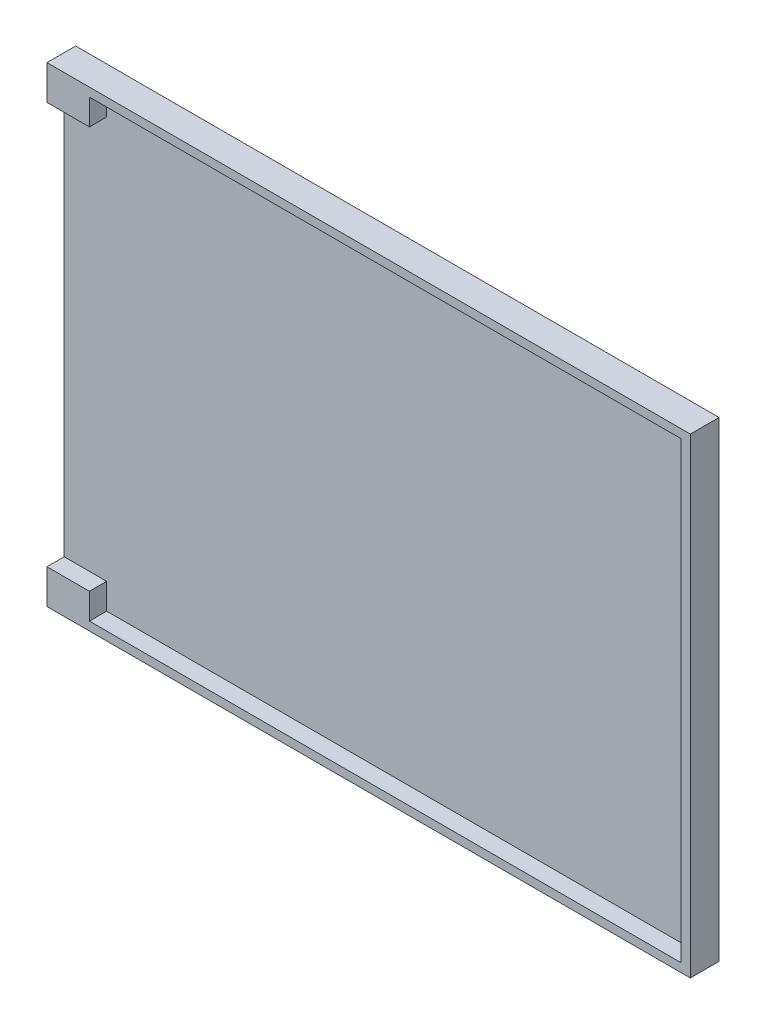
SolidWorks part; units mm, degrees
ref_plane "Front Plane" through (0, 0, 0) normal (0, 0, 1) x (1, 0, 0)
ref_plane "Top Plane" through (0, 0, 0) normal (0, 1, 0) x (1, 0, 0)
ref_plane "Right Plane" through (0, 0, 0) normal (1, 0, 0) x (0, 0, -1)
sketch "Sketch1" plane through (0, 0, 0) normal (0, 0, 1) x (1, 0, 0)
  line L0 (-33.7542, -31.1542) -> (33.4958, -31.1542) construction
  line L2 (33.4958, -31.1542) -> (33.4958, 11.3458) construction
  line L3 (-27.8542, 10.5958) -> (28.1458, 10.5958)
  line L4 (-27.8542, 10.5958) -> (-27.8542, -30.4042)
  line L5 (-27.8542, -30.4042) -> (28.1458, -30.4042)
  line L6 (28.1458, 10.5958) -> (28.1458, -30.4042)
  point P6 (0, 0)
  dimension "D1" = 41
  dimension "D2" = 56
  dimension "D3" = 0.75
  dimension "D4" = 5.35
extrude "Boss-Extrude1" add sketch "Sketch1" along normal blind 2.5
sketch "Sketch2" plane through (0, 0, 2.5) normal (0, 0, 1) x (1, 0, 0)
  line L1 (-24.1542, 9.8458) -> (27.3458, 9.8458)
  line L2 (-24.1542, 9.8458) -> (-24.1542, -29.6542)
  line L3 (-24.1542, -29.6542) -> (27.3458, -29.6542)
  line L4 (27.3458, 9.8458) -> (27.3458, -29.6542)
  line L5 (28.1458, 10.5958) -> (28.1458, -30.4042) construction
  point P4 (28.1458, -9.9042)
  point P5 (27.3458, -9.9042)
  dimension "D1" = 39.5
  dimension "D2" = 51.5
  dimension "D3" = 0.8
extrude "Cut-Extrude1" cut sketch "Sketch2" against normal blind 1.5
sketch "Sketch3" plane through (0, 0, 2.5) normal (0, 0, 1) x (1, 0, 0)
  line L0 (-27.8542, 10.5958) -> (-27.8542, -30.4042) construction
  line L1 (-27.8542, 7.5958) -> (-24.1542, 7.5958)
  line L2 (-27.8542, 7.5958) -> (-27.8542, -27.4042)
  line L3 (-27.8542, -27.4042) -> (-24.1542, -27.4042)
  line L4 (-24.1542, 7.5958) -> (-24.1542, -27.4042)
  line L5 (-24.1542, 9.8458) -> (-24.1542, -29.6542) construction
  line L6 (-22.9381, 10.5958) -> (-22.9381, -30.4042) construction
  line L7 (28.1458, 10.5958) -> (-27.8542, 10.5958) construction
  line L8 (-27.8542, -30.4042) -> (28.1458, -30.4042) construction
  point P14 (-22.9381, -9.9042)
  point P15 (-27.8542, -9.9042)
  dimension "D1" = 35
extrude "Cut-Extrude2" cut sketch "Sketch3" against normal blind 1.5
